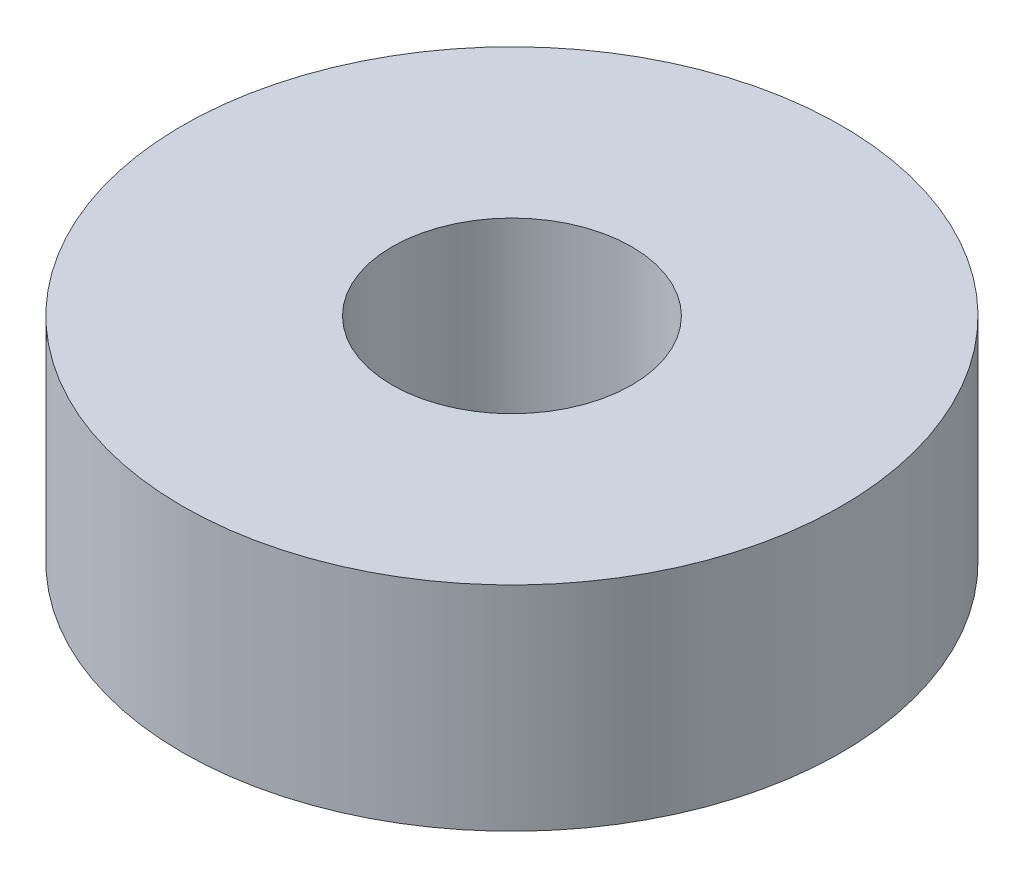
SolidWorks part; units mm, degrees
ref_plane "Front Plane" through (0, 0, 0) normal (0, 0, 1) x (1, 0, 0)
ref_plane "Top Plane" through (0, 0, 0) normal (0, 1, 0) x (1, 0, 0)
ref_plane "Right Plane" through (0, 0, 0) normal (1, 0, 0) x (0, 0, -1)
sketch "Sketch1" plane through (0, 0, 0) normal (0, 1, 0) x (1, 0, 0)
  circle A0 centre (0, 0) radius 11
  circle A1 centre (0, 0) radius 4
  dimension "D1" = 22
  dimension "D2" = 8
extrude "Boss-Extrude1" add sketch "Sketch1" along normal blind 7.12
